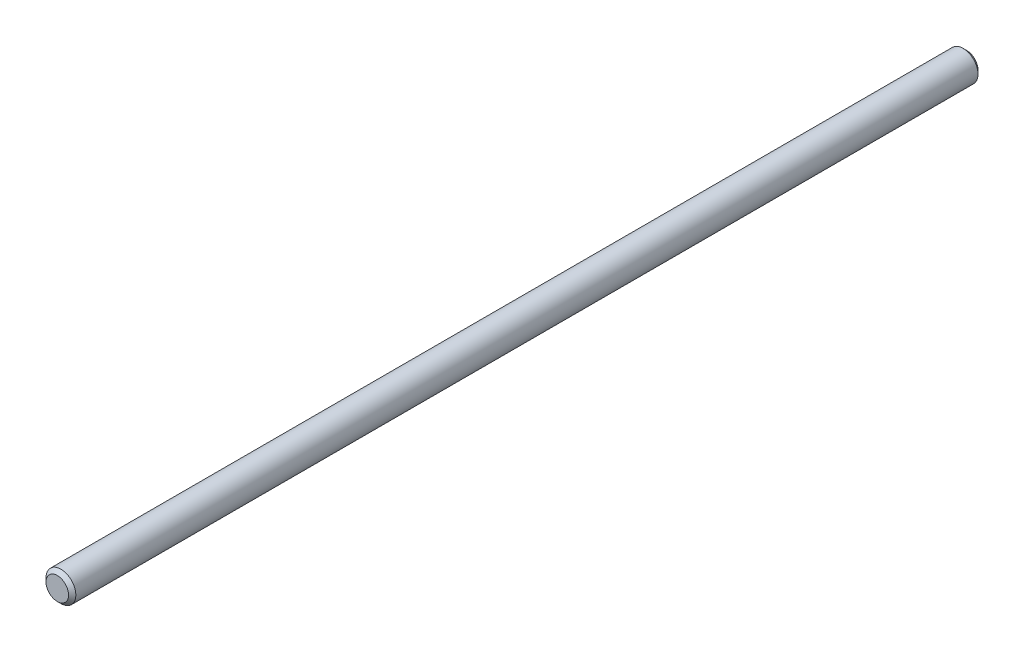
SolidWorks part; units mm, degrees
ref_plane "Front Plane" through (0, 0, 0) normal (0, 0, 1) x (1, 0, 0)
ref_plane "Top Plane" through (0, 0, 0) normal (0, 1, 0) x (1, 0, 0)
ref_plane "Right Plane" through (0, 0, 0) normal (1, 0, 0) x (0, 0, -1)
sketch "Sketch1" plane through (0, 0, 0) normal (0, 0, 1) x (1, 0, 0)
  circle A0 centre (0, 0) radius 4.1
  dimension "D1" = 8.2
extrude "Boss-Extrude1" add sketch "Sketch1" along normal blind 250
chamfer "Chamfer1" distance 1 angle 45 2 edges at (4.1, 0, 0) (4.1, 0, 250)
